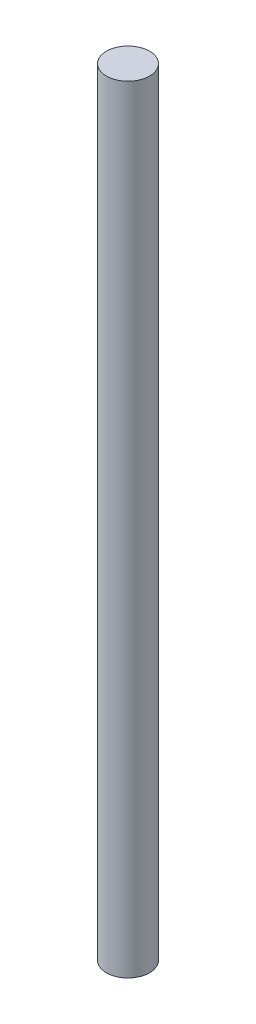
SolidWorks part; units mm, degrees
material "Plain Carbon Steel"
ref_plane "Front Plane" through (0, 0, 0) normal (0, 0, 1) x (1, 0, 0)
ref_plane "Top Plane" through (0, 0, 0) normal (0, 1, 0) x (1, 0, 0)
ref_plane "Right Plane" through (0, 0, 0) normal (1, 0, 0) x (0, 0, -1)
sketch "Sketch1" plane through (0, 0, 0) normal (0, 1, 0) x (1, 0, 0)
  circle A0 centre (0, 0) radius 3.175
  dimension "D1" = 6.35
extrude "Boss-Extrude1" add sketch "Sketch1" along normal blind 114.3
